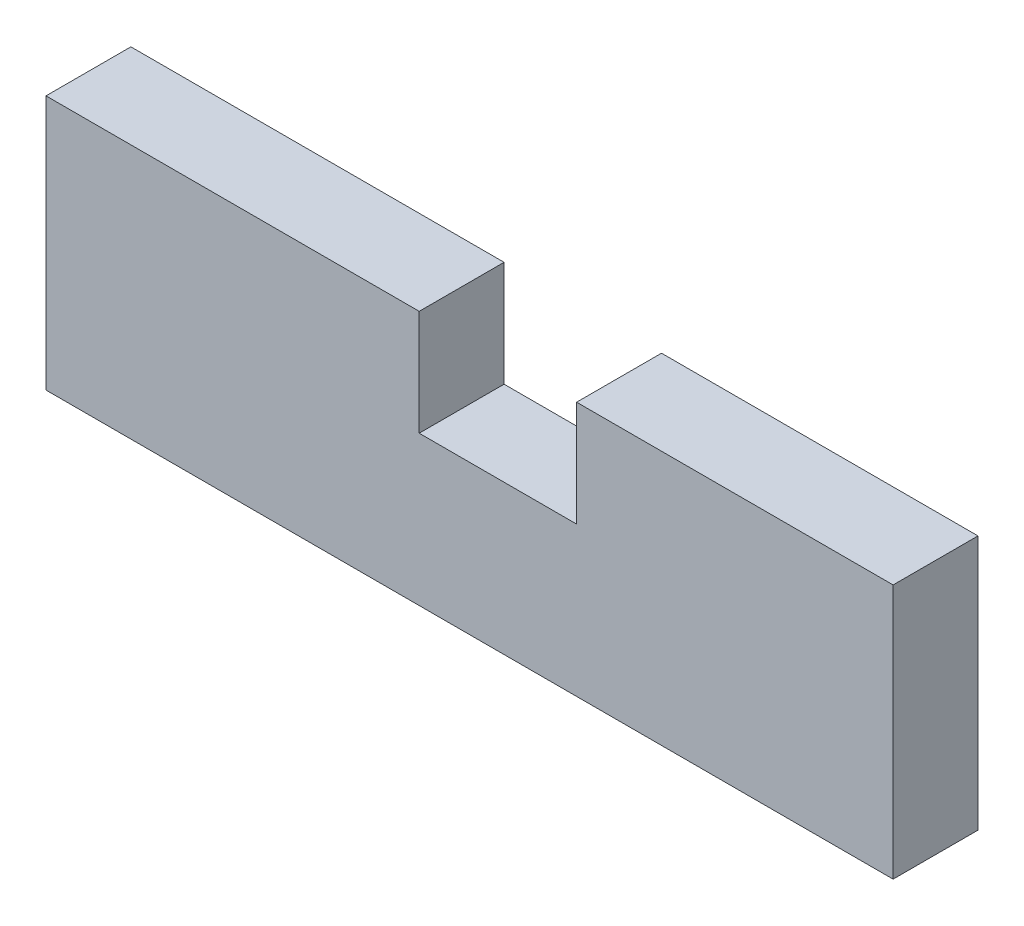
SolidWorks part; units mm, degrees
ref_plane "Спереди" through (0, 0, 0) normal (0, 0, 1) x (1, 0, 0)
ref_plane "Сверху" through (0, 0, 0) normal (0, 1, 0) x (1, 0, 0)
ref_plane "Справа" through (0, 0, 0) normal (1, 0, 0) x (0, 0, -1)
sketch "Эскиз1" plane through (0, 0, 0) normal (0, 0, 1) x (1, 0, 0)
  line L0 (0, 0) -> (199.571, 0)
  line L1 (199.571, 0) -> (199.571, 60.0362)
  line L2 (199.571, 60.0362) -> (125.0074, 60.0362)
  line L3 (125.0074, 60.0362) -> (125.0074, 35.1653)
  line L4 (125.0074, 35.1653) -> (87.9224, 35.1653)
  line L5 (87.9224, 35.1653) -> (87.9224, 60.0362)
  line L6 (87.9224, 60.0362) -> (0, 60.0362)
  line L7 (0, 60.0362) -> (0, 0)
extrude "Бобышка-Вытянуть1" add sketch "Эскиз1" along normal blind 20
